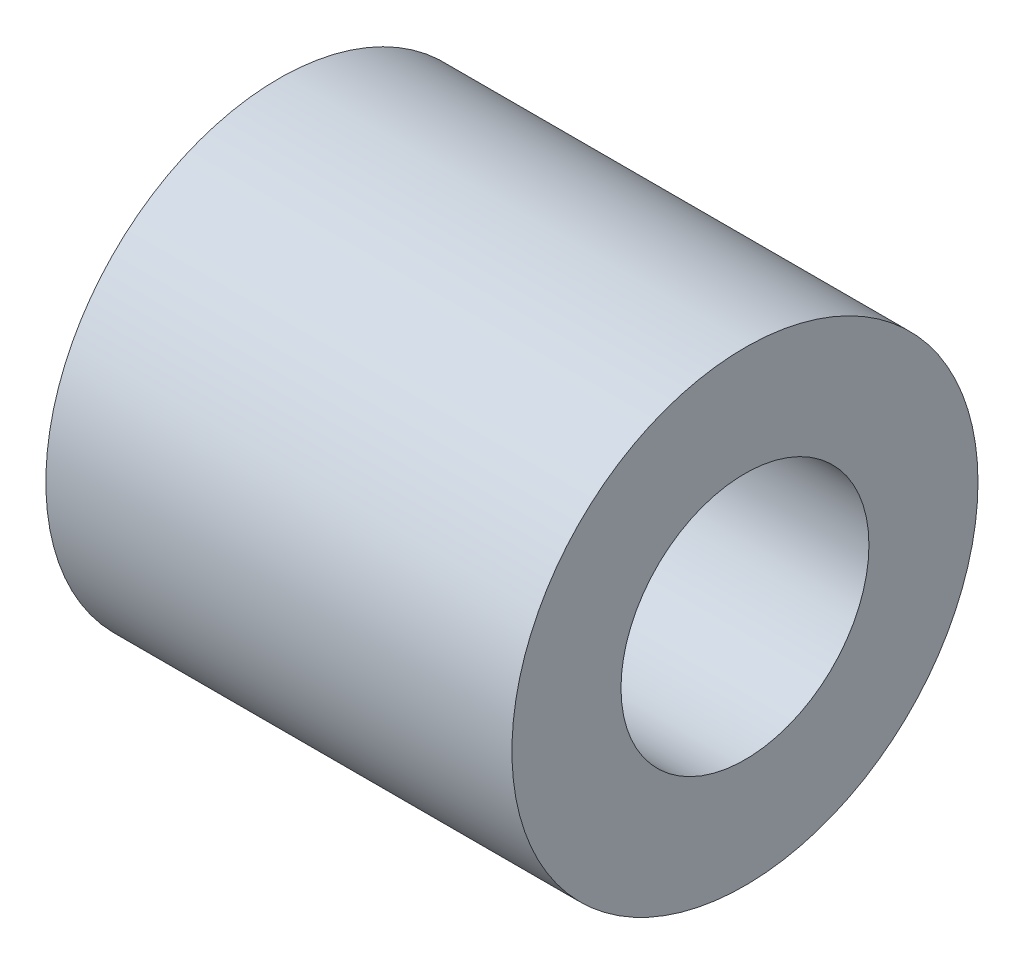
SolidWorks part; units mm, degrees
material "Delrin 2700 NC010, Low Viscosity Acetal Copolymer (SS)"
ref_plane "Front Plane" through (0, 0, 0) normal (0, 0, 1) x (1, 0, 0)
ref_plane "Top Plane" through (0, 0, 0) normal (0, 1, 0) x (1, 0, 0)
ref_plane "Right Plane" through (0, 0, 0) normal (1, 0, 0) x (0, 0, -1)
sketch "Sketch1" plane through (0, 0, 0) normal (1, 0, 0) x (0, 0, -1)
  circle A0 centre (0, 0) radius 3.3782
  circle A1 centre (0, 0) radius 6.35
  dimension "D1" = 6.7564
  dimension "D2" = 12.7
extrude "Boss-Extrude1" add sketch "Sketch1" along normal blind 12.7
